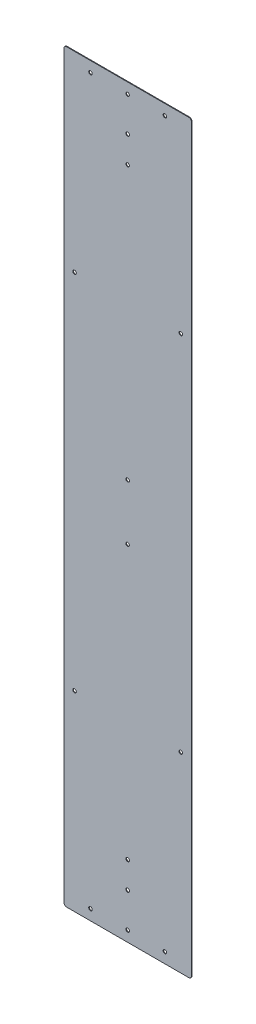
SolidWorks part; units mm, degrees
material "Acrylic (Medium-high impact)"
ref_plane "Front Plane" through (0, 0, 0) normal (0, 0, 1) x (1, 0, 0)
ref_plane "Top Plane" through (0, 0, 0) normal (0, 1, 0) x (1, 0, 0)
ref_plane "Right Plane" through (0, 0, 0) normal (1, 0, 0) x (0, 0, -1)
sketch "Sketch1" plane through (0, 0, 0) normal (0, 0, 1) x (1, 0, 0)
  line L1 (-152.4, 890.5875) -> (152.4, 890.5875)
  line L2 (-152.4, 890.5875) -> (-152.4, -890.5875)
  line L3 (-152.4, -890.5875) -> (152.4, -890.5875)
  line L4 (152.4, 890.5875) -> (152.4, -890.5875)
  line L5 (-152.4, 890.5875) -> (152.4, -890.5875) construction
  line L6 (-152.4, -890.5875) -> (152.4, 890.5875) construction
  point P0 (0, 0)
  dimension "D1" = 1781.175
  dimension "D2" = 304.8
extrude "Boss-Extrude1" add sketch "Sketch1" along normal blind 1.5875
sketch "Sketch2" plane through (0, 0, 1.5875) normal (0, 0, 1) x (1, 0, 0)
  line L0 (-152.4, 0) -> (152.4, 0) construction
  line L1 (-152.4, 890.5875) -> (-152.4, -890.5875) construction
  line L2 (152.4, -890.5875) -> (152.4, 890.5875) construction
  line L3 (152.4, 890.5875) -> (-152.4, 890.5875) construction
  line L4 (88.9, 865.1875) -> (-88.9, 865.1875)
  line L5 (88.9, -865.1875) -> (-88.9, -865.1875)
  point P0 (0, 865.1875)
  point P3 (0, 66.675)
  point P4 (-127, 433.3875)
  point P6 (127, 433.3875)
  point P12 (0, 719.1375)
  point P15 (0, -865.1875)
  point P16 (127, -433.3875)
  point P17 (-127, -433.3875)
  point P18 (0, -66.675)
  point P19 (0, -719.1375)
  point P20 (0, -782.6375)
  point P21 (0, 782.6375)
  point P24 (0, 865.1875)
  dimension "D1" = 25.4
  dimension "D2" = 25.4
  dimension "D3" = 25.4
  dimension "D4" = 66.675
  dimension "D5" = 457.2
  dimension "D6" = 63.5
  dimension "D7" = 107.95
  dimension "D8" = 177.8
hole_wizard "5/16 Clearance Hole1" positions "Sketch3" profile "Sketch4" hole size "5/16" standard "ANSI Inch" end condition up to next
sketch "Sketch3" plane through (0, 0, 1.5875) normal (0, 0, 1) x (1, 0, 0)
  point P0 (0, 865.1875)
  point P3 (-127, 433.3875)
  point P6 (127, 433.3875)
  point P9 (0, 66.675)
  point P12 (0, -66.675)
  point P15 (-127, -433.3875)
  point P18 (127, -433.3875)
  point P21 (0, -865.1875)
  point P25 (0, 782.6375)
  point P28 (0, 719.1375)
  point P31 (0, -782.6375)
  point P34 (0, -719.1375)
  point P37 (-88.9, 865.1875)
  point P40 (88.9, 865.1875)
  point P43 (-88.9, -865.1875)
  point P46 (88.9, -865.1875)
sketch "Sketch4" plane through (0, 865.1875, 1.5875) normal (1, 0, 0) x (0, -1, 0)
  line L0 (0, 0) -> (0, 1.5875)
  line L1 (0, 1.5875) -> (4.2164, 1.5875)
  line L2 (4.2164, 1.5875) -> (4.2164, 0)
  line L5 (4.2164, 0) -> (0, 0)
  line L11 (0, -6.35) -> (0, 107.95) construction
  dimension "Thru Hole Dia." = 8.4328
  dimension "Thru Hole Depth" = 1.5875
sketch "Sketch5" plane through (0, 0, 1.5875) normal (0, 0, 1) x (1, 0, 0)
  line L0 (152.4, -890.5875) -> (152.4, 890.5875) construction
  line L1 (152.4, -558.8) -> (0, -558.8)
  line L2 (152.4, -558.8) -> (152.4, -279.4)
  line L3 (152.4, -279.4) -> (0, -279.4)
  line L4 (0, -558.8) -> (0, -279.4)
  line L5 (-152.4, 0) -> (152.4, 0) construction
  dimension "D1" = 558.8
  dimension "D2" = 279.4
  dimension "D3" = 152.4
sketch "Sketch7" plane through (0, 0, 1.5875) normal (0, 0, 1) x (1, 0, 0)
  line L4 (0, -558.8) -> (152.4, -558.8)
  line L5 (0, -279.4) -> (0, -558.8)
  line L6 (152.4, -279.4) -> (0, -279.4)
  line L7 (152.4, -558.8) -> (152.4, -279.4)
  line L8 (0, -558.8) -> (152.4, -558.8)
  line L9 (0, -279.4) -> (0, -558.8)
  line L10 (152.4, -279.4) -> (0, -279.4)
  line L11 (152.4, -558.8) -> (152.4, -279.4)
  dimension "D1" = 0
extrude "Cut-Extrude2" [suppressed] cut sketch "Sketch7" against normal through all
fillet "Fillet1" [suppressed] radius 12.7
sketch "Sketch8" plane through (0, 0, 1.5875) normal (0, 0, 1) x (1, 0, 0)
  line L0 (0, -55) -> (0, 55) construction
  line L1 (-152.4, -558.8) -> (-152.4, -279.4) construction
  line L2 (-152.4, -279.4) -> (0, -279.4)
  line L3 (0, -279.4) -> (0, -558.8)
  line L4 (0, -558.8) -> (152.4, -558.8)
  line L5 (0, -279.4) -> (0, -558.8)
  line L6 (152.4, -279.4) -> (0, -279.4)
  line L7 (152.4, -558.8) -> (152.4, -279.4)
  line L8 (-152.4, -558.8) -> (152.4, -558.8) construction
  line L9 (0, -279.4) -> (0, -558.8) construction
  line L10 (152.4, -279.4) -> (-152.4, -279.4) construction
  line L11 (152.4, -558.8) -> (152.4, -279.4) construction
  line L12 (0, -558.8) -> (-152.4, -558.8)
  line L13 (-152.4, -558.8) -> (-152.4, -279.4)
  dimension "D1" = 0
extrude "Cut-Extrude3" [suppressed] cut sketch "Sketch8" against normal through all
fillet "Fillet2" [suppressed] radius 12.7
sketch "Sketch9" [suppressed] plane through (0, 0, 3.175) normal (0, 0, 1) x (1, 0, 0)
  line L0 (-152.4, 890.5875) -> (-152.4, -890.5875) construction
  line L1 (-152.4, -279.4) -> (50.8, -279.4)
  line L2 (-152.4, -279.4) -> (-152.4, -558.8)
  line L3 (-152.4, -558.8) -> (50.8, -558.8)
  line L4 (50.8, -279.4) -> (50.8, -558.8)
  line L5 (152.4, -558.8) -> (0, -558.8) construction
  line L6 (152.4, -279.4) -> (0, -279.4) construction
  dimension "D1" = 203.2
extrude "Cut-Extrude4" [suppressed] cut sketch "Sketch9" against normal through all
fillet "Fillet3" [suppressed] radius 12.7
fillet "Fillet4" radius 6.35 4 edges at (-152.4, 890.5875, 0.7937) (152.4, 890.5875, 0.7937) (152.4, -890.5875, 0.7937) (-152.4, -890.5875, 0.7937)
